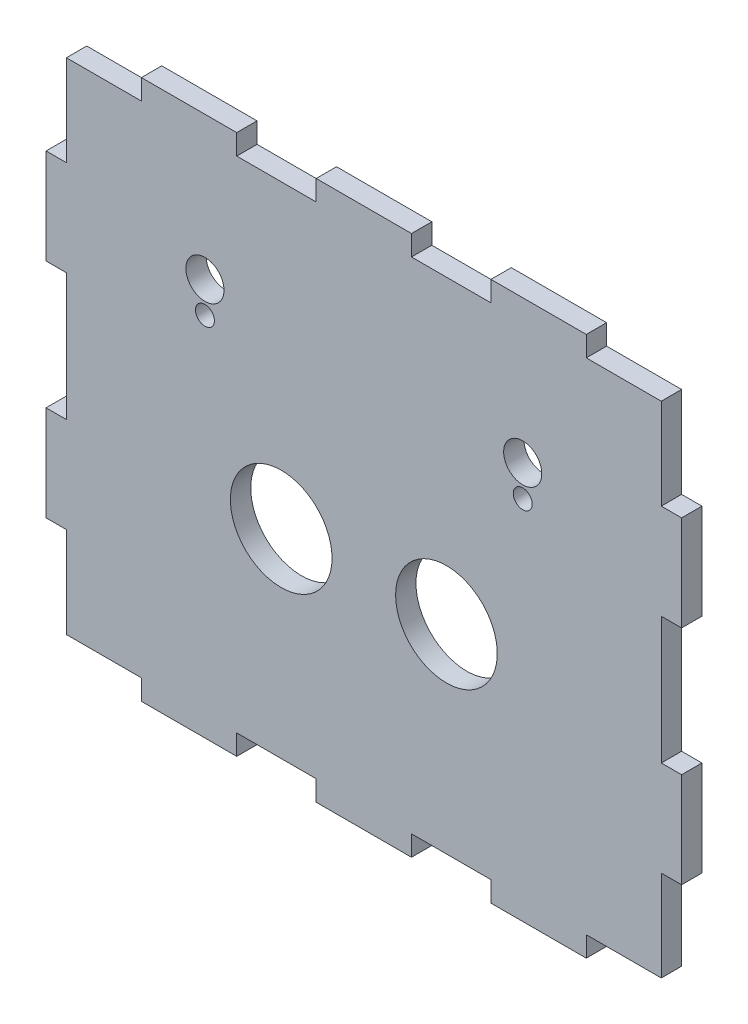
SolidWorks part; units mm, degrees
ref_plane "Front Plane" through (0, 0, 0) normal (0, 0, 1) x (1, 0, 0)
ref_plane "Top Plane" through (0, 0, 0) normal (0, 1, 0) x (1, 0, 0)
ref_plane "Right Plane" through (0, 0, 0) normal (1, 0, 0) x (0, 0, -1)
sketch "Sketch1" plane through (0, 0, 0) normal (0, 0, 1) x (1, 0, 0)
  line L0 (-50, 10) -> (-50, 25)
  line L1 (55, 0) -> (-55, 0) construction
  line L2 (0, -54.3667) -> (0, 54.3667) construction
  line L3 (0, -55) -> (0, 55) construction
  line L4 (-46.8, 39.3) -> (-46.8, 25)
  line L5 (-46.8, 25) -> (-50, 25)
  line L6 (-50, 10) -> (-46.8, 10)
  line L7 (-46.8, 10) -> (-46.8, -10)
  line L8 (-46.8, 39.3) -> (-35, 39.3)
  line L9 (-35, 39.3) -> (-35, 42.5)
  line L10 (-20, 42.5) -> (-20, 39.3)
  line L11 (-20, 39.3) -> (-7.5, 39.3)
  line L12 (-7.5, 39.3) -> (-7.5, 42.5)
  line L13 (-7.5, 42.5) -> (7.5, 42.5)
  line L14 (-35, 42.5) -> (-20, 42.5)
  line L15 (35, 42.5) -> (20, 42.5)
  line L16 (7.5, 39.3) -> (7.5, 42.5)
  line L17 (20, 39.3) -> (7.5, 39.3)
  line L18 (20, 42.5) -> (20, 39.3)
  line L19 (35, 39.3) -> (35, 42.5)
  line L20 (46.8, 39.3) -> (35, 39.3)
  line L21 (46.8, 10) -> (46.8, -10)
  line L22 (50, 10) -> (46.8, 10)
  line L23 (46.8, 25) -> (50, 25)
  line L24 (46.8, 39.3) -> (46.8, 25)
  line L25 (50, 10) -> (50, 25)
  line L26 (0, 0) -> (46.8, 0) construction
  line L27 (50, -10) -> (50, -25)
  line L28 (46.8, -39.3) -> (46.8, -25)
  line L29 (46.8, -25) -> (50, -25)
  line L30 (50, -10) -> (46.8, -10)
  line L31 (46.8, -39.3) -> (35, -39.3)
  line L32 (35, -39.3) -> (35, -42.5)
  line L33 (20, -42.5) -> (20, -39.3)
  line L34 (20, -39.3) -> (7.5, -39.3)
  line L35 (7.5, -39.3) -> (7.5, -42.5)
  line L36 (35, -42.5) -> (20, -42.5)
  line L37 (-35, -42.5) -> (-20, -42.5)
  line L38 (-7.5, -42.5) -> (7.5, -42.5)
  line L39 (-7.5, -39.3) -> (-7.5, -42.5)
  line L40 (-20, -39.3) -> (-7.5, -39.3)
  line L41 (-20, -42.5) -> (-20, -39.3)
  line L42 (-35, -39.3) -> (-35, -42.5)
  line L43 (-46.8, -39.3) -> (-35, -39.3)
  line L44 (-50, -10) -> (-46.8, -10)
  line L45 (-46.8, -25) -> (-50, -25)
  line L46 (-46.8, -39.3) -> (-46.8, -25)
  line L47 (-50, -10) -> (-50, -25)
  circle A0 centre (-13, -8) radius 8
  circle A1 centre (-25, 20) radius 3
  circle A2 centre (-25, 15.1) radius 1.49
  circle A3 centre (13, -8) radius 8
  circle A4 centre (25, 15.1) radius 1.49
  circle A5 centre (25, 20) radius 3
  point P23 (0, 42.5)
  point P52 (-46.8, 0)
  point P55 (0, -42.5)
  dimension "D9" = 16
  dimension "D12" = 6
  dimension "D15" = 2.98
  dimension "D1" = 50
  dimension "D2" = 42.5
  dimension "D3" = 15
  dimension "D4" = 10
  dimension "D5" = 3.2
  dimension "D6" = 15
  dimension "D7" = 7.5
  dimension "D8" = 15
  dimension "D10" = 13
  dimension "D11" = 8
  dimension "D13" = 25
  dimension "D14" = 20
  dimension "D16" = 4.9
extrude "Boss-Extrude1" add sketch "Sketch1" along normal blind 3.2
